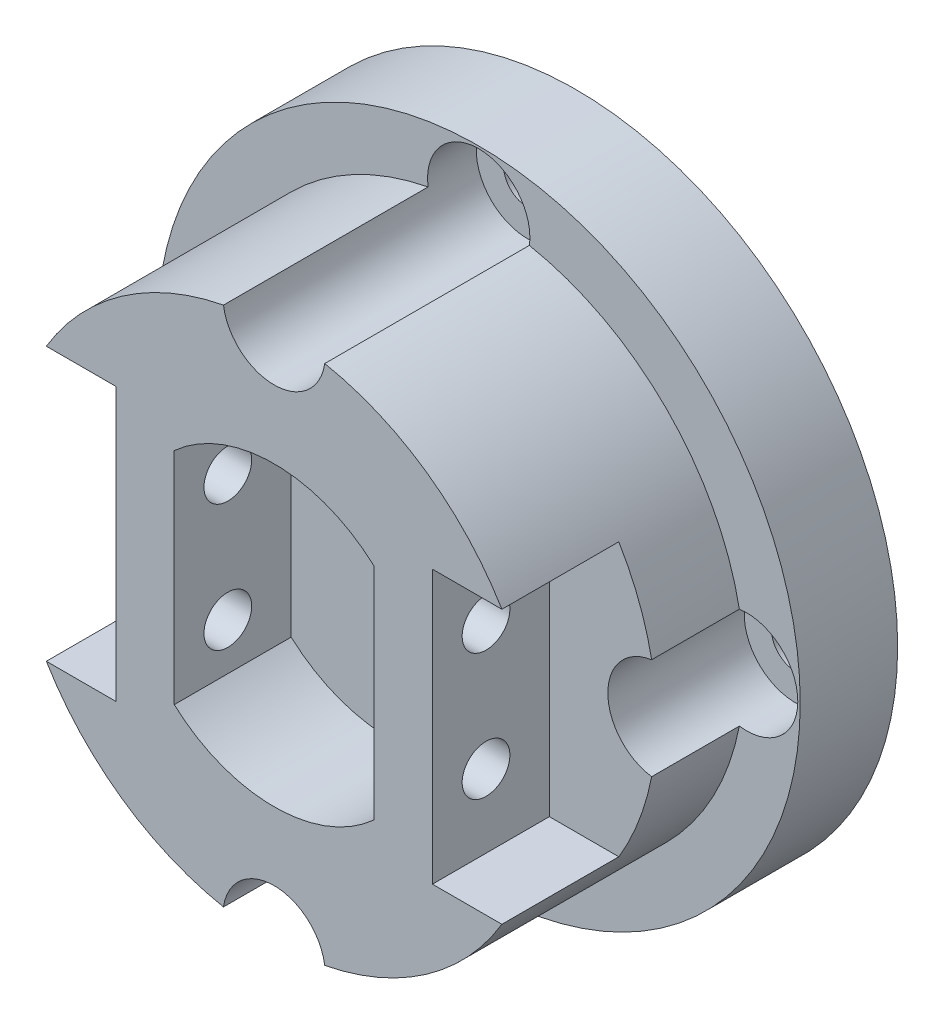
SolidWorks part; units mm, degrees
ref_plane "Front Plane" through (0, 0, 0) normal (0, 0, 1) x (1, 0, 0)
ref_plane "Top Plane" through (0, 0, 0) normal (0, 1, 0) x (1, 0, 0)
ref_plane "Right Plane" through (0, 0, 0) normal (1, 0, 0) x (0, 0, -1)
sketch "Sketch1" plane through (0, 0, 0) normal (0, 0, 1) x (1, 0, 0)
  circle A0 centre (0, 0) radius 33
  dimension "D1" = 66
extrude "Extrude1" add sketch "Sketch1" along normal blind 10
sketch "Sketch2" plane through (0, 0, 10) normal (0, 0, 1) x (1, 0, 0)
  circle A0 centre (0, 0) radius 27.25
  dimension "D1" = 54.5
extrude "Extrude2" add sketch "Sketch2" along normal blind 21
sketch "Sketch3" plane through (0, 0, 31) normal (0, 0, 1) x (1, 0, 0)
  line L0 (-10.25, 11.2916) -> (-10.25, -11.2916)
  line L1 (10.25, 11.2916) -> (10.25, -11.2916)
  line L2 (-10.25, 0) -> (10.25, 0) construction
  arc A0 (-10.25, -11.2916) -> (10.25, -11.2916) centre (0, 0) ccw
  arc A1 (10.25, 11.2916) -> (-10.25, 11.2916) centre (0, 0) ccw
  point P9 (0, 0)
  dimension "D1" = 30.5
  dimension "D2" = 20.5
extrude "Extrude3" cut sketch "Sketch3" against normal blind 12
sketch "Sketch4" plane through (0, 0, 0) normal (0, 0, -1) x (-1, 0, 0)
  line L0 (0, 27.5) -> (0, -27.5) construction
  line L2 (27.5, 0) -> (-27.5, 0) construction
  circle A0 centre (0, 27.5) radius 2.45
  circle A1 centre (-27.5, 0) radius 2.45
  circle A2 centre (0, -27.5) radius 2.45
  circle A3 centre (27.5, 0) radius 2.45
  point P4 (0, 0)
  point P6 (0, 0)
  dimension "D1" = 4.9
  dimension "D2" = 55
extrude "Extrude4" cut sketch "Sketch4" against normal blind 36
sketch "Sketch5" plane through (10.25, 0, 0) normal (-1, 0, 0) x (0, 0, 1)
  line L1 (19, -11.2916) -> (19, 11.2916) construction
  line L2 (31, 0) -> (19, 0) construction
  line L3 (31, -11.2916) -> (31, 11.2916) construction
  line L4 (25.5, 6.5) -> (25.5, -6.5) construction
  circle A0 centre (25.5, 6.5) radius 2.45
  circle A1 centre (25.5, -6.5) radius 2.45
  point P10 (25.5, 0)
  dimension "D2" = 4.9
  dimension "D1" = 13
  dimension "D3" = 6.5
extrude "Extrude5" cut sketch "Sketch5" against normal blind 38 and the other way blind 38
sketch "Sketch6" plane through (0, 0, 31) normal (0, 0, 1) x (1, 0, 0)
  line L0 (-10.25, 11.2916) -> (-10.25, -11.2916) construction
  line L1 (-16.25, 14) -> (-36.1446, 14)
  line L2 (-16.25, 14) -> (-16.25, -14)
  line L3 (-16.25, -14) -> (-36.1446, -14)
  line L4 (-36.1446, 14) -> (-36.1446, -14)
  line L5 (0, 0) -> (-27.25, 0) construction
  circle A0 centre (0, 0) radius 27.25 construction
  point P12 (-16.25, 0)
  dimension "D1" = 6
  dimension "D2" = 28
extrude "Extrude6" cut sketch "Sketch6" against normal blind 12
mirror "Mirror1" about plane through (0, 0, 0) normal (1, 0, 0) of "Extrude6"
sketch "Sketch8" plane through (0, 0, 31) normal (0, 0, 1) x (1, 0, 0)
  circle A0 centre (0, 27.5) radius 5.25
  circle A1 centre (27.5, 0) radius 5.25
  circle A2 centre (-27.5, 0) radius 5.25
  circle A3 centre (0, -27.5) radius 5.25
  dimension "D1" = 10.5
extrude "Extrude7" cut sketch "Sketch8" against normal offset from surface (26 mm away) 5 up to face at (-29.95, 0, 0)
